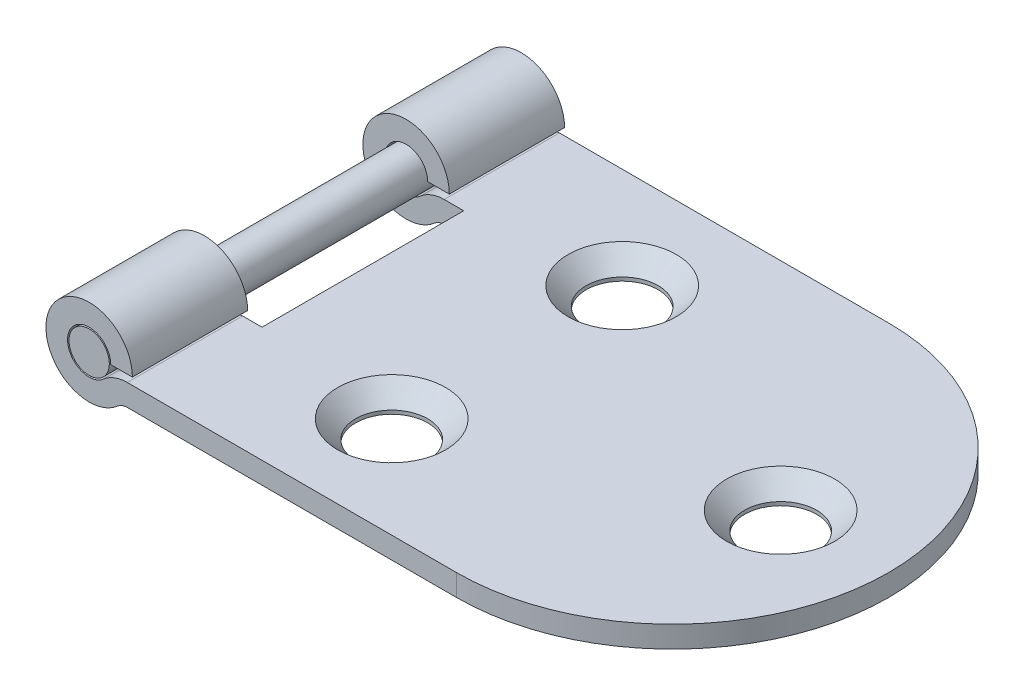
SolidWorks part; units mm, degrees
material "SUS304"
ref_plane "正面" through (0, 0, 0) normal (0, 0, 1) x (1, 0, 0)
ref_plane "平面" through (0, 0, 0) normal (0, 1, 0) x (1, 0, 0)
ref_plane "右側面" through (0, 0, 0) normal (1, 0, 0) x (0, 0, -1)
sketch "ｽｹｯﾁ1" plane through (0, 0, 0) normal (0, 0, 1) x (1, 0, 0)
  line L0 (2.6458, 1.5) -> (40.5, 1.5)
  line L1 (2.6458, 0) -> (40.5, 0)
  line L4 (40.5, 0) -> (40.5, 1.5)
  line L5 (1.5, 2) -> (3, 2)
  arc A0 (1.5, 2) -> (0.9922, 0.875) centre (0, 2) ccw
  arc A2 (3, 2) -> (1.9843, -0.25) centre (0, 2) ccw
  arc A3 (2.6458, 0) -> (1.9843, -0.25) centre (2.6458, -1) ccw
  arc A4 (2.6458, 1.5) -> (0.9922, 0.875) centre (2.6458, -1) ccw
  dimension "D1" = 1.5
  dimension "D3" = 3
  dimension "D4" = 3
  dimension "D5" = 1
  dimension "D6" = 2.5
  dimension "D2" = 2
  dimension "D7" = 40.5
  dimension "D8" = 1.5
extrude "BODY" add sketch "ｽｹｯﾁ1" along normal mid plane 30 separate body
sketch "ｽｹｯﾁ2" plane through (0, 1.5, 0) normal (0, 1, 0) x (1, 0, 0)
  line L0 (40.5, 15) -> (2.6458, 15) construction
  line L1 (40.5, -15) -> (2.6458, -15) construction
  line L2 (40.5, -15) -> (40.5, 15) construction
  line L3 (25.5, 15) -> (40.5, 15)
  line L4 (40.5, 15) -> (40.5, -15)
  line L5 (40.5, -15) -> (25.5, -15)
  arc A0 (25.5, -15) -> (25.5, 15) centre (25.5, 0) ccw
  circle A1 centre (33, 0) radius 2.5
  circle A2 centre (14, 8) radius 2.5
  circle A3 centre (14, -8) radius 2.5
  line M3 (40.5, 15) -> (2.6458, 15)
  line M5 (2.6458, -15) -> (40.5, -15)
  line M6 (40.5, -15) -> (40.5, 15)
  dimension "D1" = 5
  dimension "D2" = 7.5
  dimension "D3" = 19
  dimension "D4" = 8
  dimension "D5" = 8
extrude "CUT-1" cut sketch "ｽｹｯﾁ2" against normal blind 30 contours A1 | A2 | A3 | A0 M5 M6 | A0 L4 M3
hole_wizard "φ7.5-φ5" positions "3Dｽｹｯﾁ1" profile "ｽｹｯﾁ3" countersink size "M5" standard "ISO"
sketch3d "3Dｽｹｯﾁ1"
  line L0 (14, 0, -8) -> (14, 1.5, -8) construction
  line L1 (14, 0, 8) -> (14, 1.5, 8) construction
  line L2 (33, 0, 0) -> (33, 1.5, 0) construction
  point P0 (14, 1.5, -8)
  point P4 (14, 1.5, 8)
  point P8 (33, 1.5, 0)
sketch "ｽｹｯﾁ3" plane through (14, 1.5, -8) normal (1, 0, 0) x (0, 0, 1)
  line L0 (0, 0) -> (0, 10.0022)
  line L1 (0, 10.0022) -> (2.5, 8.5)
  line L2 (2.5, 8.5) -> (2.5, 1.25)
  line L3 (2.5, 1.25) -> (3.75, 0)
  line L5 (3.75, 0) -> (0, 0)
  line L6 (-2.5, 1.25) -> (-3.75, 0) construction
  line L10 (0, 10.0022) -> (-2.5, 8.5) construction
  line L11 (0, -6.35) -> (0, 107.95) construction
  dimension "穴の直径" = 5
  dimension "穴の深さ" = 8.5
  dimension "表面の皿穴の直径" = 7.5
  dimension "表面の皿穴の角度" = 90
  dimension "ﾄﾞﾘﾙ角度" = 118
sketch "ｽｹｯﾁ4" plane through (0, 1.5, 0) normal (0, 1, 0) x (1, 0, 0)
  line L0 (0, 7) -> (0, -7) construction
  line L2 (-4, 7) -> (4, 7)
  line L3 (-4, 7) -> (-4, -7)
  line L4 (-4, -7) -> (4, -7)
  line L5 (4, 7) -> (4, -7)
  point P2 (0, 0)
  dimension "D1" = 14
  dimension "D2" = 4
extrude "ｶｯﾄ - 押し出し2" cut sketch "ｽｹｯﾁ4" against normal mid plane 30
sketch "ｽｹｯﾁ5" [suppressed] plane through (0, 1.5, 0) normal (0, 1, 0) x (1, 0, 0)
  line L0 (25.5, -15) -> (2.6458, -15) construction
  line L1 (-4, -7) -> (4, -7)
  line L2 (-4, -7) -> (-4, -15)
  line L3 (-4, -15) -> (4, -15)
  line L4 (4, 7) -> (-4, 7)
  line L5 (4, -7) -> (4, 7)
  line L6 (-4, -7) -> (4, -7)
  line L7 (-4, 7) -> (-4, -7)
  line L8 (4, 7) -> (-4, 7)
  line L9 (4, -7) -> (4, 7) construction
  line L10 (-4, -7) -> (4, -7)
  line L11 (-4, 7) -> (-4, -7) construction
  line L12 (4, -7) -> (4, -15)
  line L13 (25.5, 15) -> (2.6458, 15) construction
  line L14 (-4, 7) -> (4, 7)
  line L15 (-4, 7) -> (-4, 15)
  line L16 (-4, 15) -> (4, 15)
  line L17 (4, 7) -> (4, 15)
  line M14 (2.6458, 15) -> (2.6458, -15)
  dimension "D1" = 0
extrude "ｶｯﾄ - 押し出し3" [suppressed] cut sketch "ｽｹｯﾁ5" against normal mid plane 30 contours L16 L15 L8 M14 | L2 L3 L1 M14
sketch "ｽｹｯﾁ6" plane through (0, 0, 0) normal (0, 0, 1) x (1, 0, 0)
  circle A0 centre (0, 2) radius 1.4
  dimension "D1" = 2.8
extrude "ﾎﾞｽ - 押し出し1" add sketch "ｽｹｯﾁ6" along normal up to surface and the other way up to surface separate body contours A0 up to face at (6.981, 1.4219, 15) other way up to face at (6.981, 1.4219, -15)
